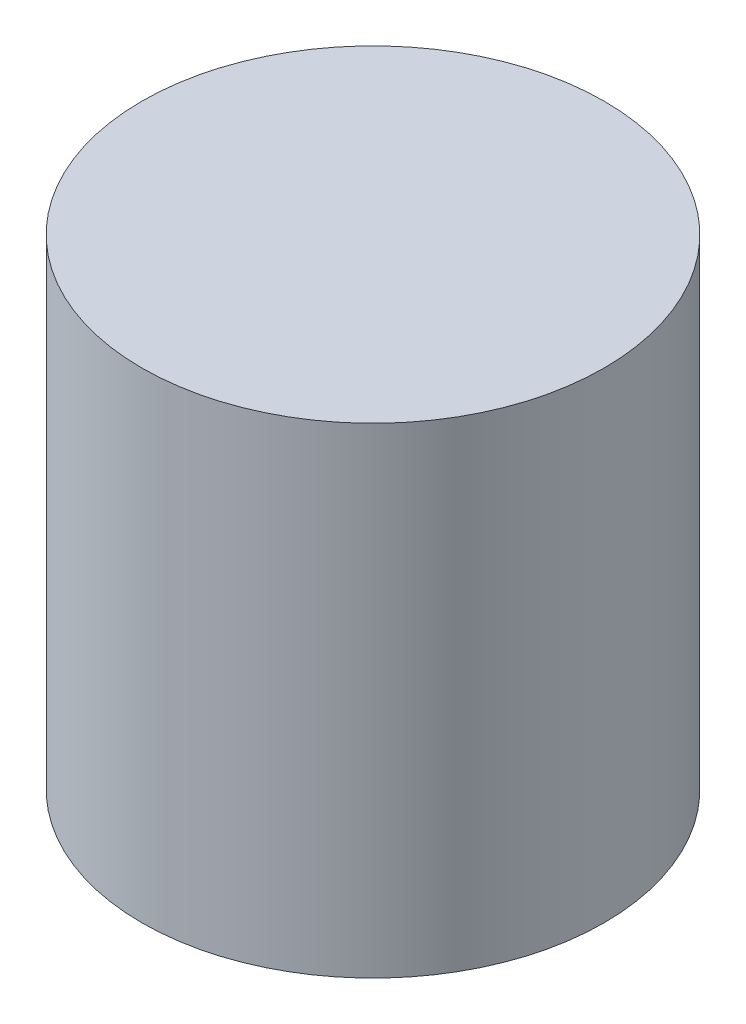
SolidWorks part; units mm, degrees
ref_plane "Front Plane" through (0, 0, 0) normal (0, 0, 1) x (1, 0, 0)
ref_plane "Top Plane" through (0, 0, 0) normal (0, 1, 0) x (1, 0, 0)
ref_plane "Right Plane" through (0, 0, 0) normal (1, 0, 0) x (0, 0, -1)
sketch "Sketch1" plane through (0, 0, 0) normal (0, 1, 0) x (1, 0, 0)
  circle A0 centre (0, 0) radius 38
  dimension "D1" = 76
extrude "Boss-Extrude1" add sketch "Sketch1" along normal blind 79
sketch "Sketch9" plane through (0, 0, 0) normal (0, -1, 0) x (1, 0, 0)
  circle A0 centre (0, 0) radius 36.5
  dimension "D1" = 73
extrude "Cut-Extrude1" cut sketch "Sketch9" against normal blind 76
